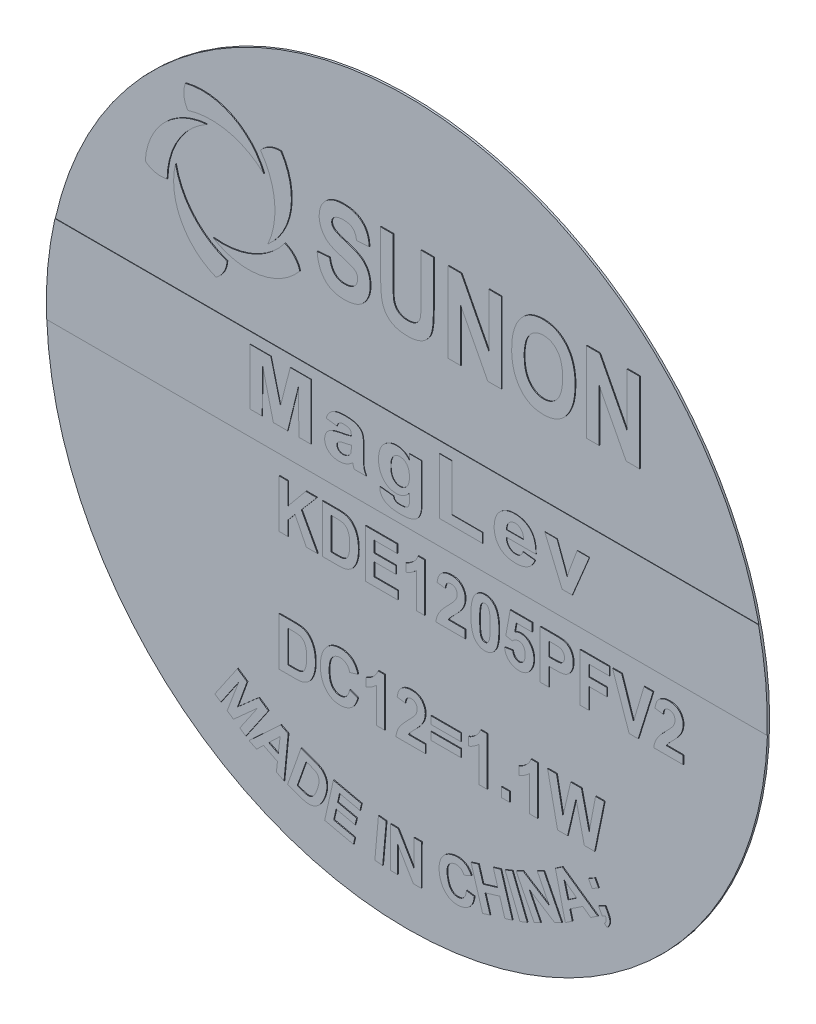
SolidWorks part; units mm, degrees
material "PET"
ref_plane "Front" through (0, 0, 0) normal (0, 0, 1) x (1, 0, 0)
ref_plane "Top" through (0, 0, 0) normal (0, 1, 0) x (1, 0, 0)
ref_plane "Right" through (0, 0, 0) normal (1, 0, 0) x (0, 0, -1)
sketch "Эскиз1" plane through (0, 0, 0) normal (0, 0, 1) x (1, 0, 0)
  circle A0 centre (0, 0) radius 9
  dimension "D1" = 18
extrude "Бобышка-Вытянуть1" add sketch "Эскиз1" along normal blind 0.05
sketch "Эскиз2" plane through (0, 0, 0.05) normal (0, 0, 1) x (1, 0, 0)
  arc A0 (-4.8588, -6.2452) -> (4.8833, -6.2452) centre (0.0123, -0.0965) ccw construction
  arc A2 (-5.5151, 6.5319) -> (-3.5562, 5.5539) centre (-5.0958, 4.9209) cw
  arc A4 (-5.4535, 5.9772) -> (-3.5562, 5.5539) centre (-4.8709, 4.1247) cw
  arc A5 (-5.5151, 6.5319) -> (-5.4535, 5.9772) centre (-4.9377, 6.3153) ccw
  circle A6 centre (-4.5148, 4.7517) radius 1.25 construction
  arc A7 (-3.1308, 6.2532) -> (-3.4556, 4.0879) centre (-4.5334, 5.3566) cw
  arc A8 (-3.1308, 6.2532) -> (-3.6393, 6.0232) centre (-3.1584, 5.6371) ccw
  arc A9 (-3.6393, 6.0232) -> (-3.4556, 4.0879) centre (-5.2212, 4.8967) cw
  arc A10 (-2.6591, 3.8995) -> (-4.8188, 3.5392) centre (-3.9453, 4.9563) cw
  arc A12 (-2.6591, 3.8995) -> (-3.035, 4.312) centre (-3.2536, 3.7353) ccw
  arc A15 (-3.035, 4.312) -> (-4.8188, 3.5392) centre (-4.5952, 5.4683) cw
  arc A16 (-4.7519, 2.7235) -> (-5.7619, 4.6662) centre (-4.1442, 4.2733) cw
  arc A17 (-4.7519, 2.7235) -> (-4.4757, 3.2084) centre (-5.0917, 3.2381) ccw
  arc A18 (-4.4757, 3.2084) -> (-5.7619, 4.6662) centre (-3.8581, 5.0496) cw
  arc A19 (-6.517, 4.3504) -> (-4.9815, 5.9113) centre (-4.8553, 4.2514) cw
  arc A20 (-6.517, 4.3504) -> (-5.9704, 4.2376) centre (-6.1326, 4.8327) ccw
  arc A21 (-5.9704, 4.2376) -> (-4.9815, 5.9113) centre (-4.0285, 4.2192) cw
  text T0 "SUNON" font "Arial Narrow" height 2
  text T1 "KDE1205PFV2\r\nDC12=1.1W" font "Arial Narrow" height 1.2
  text T2 "MADE IN CHINA;)" font "Arial Narrow" height 1
  text T3 "MagLev" font "Arial" height 1.4
  point P3 (0, 0)
  point P16 (-5.1102, 5.946)
  point P17 (-5.7604, 4.6474)
  point P40 (-4.5148, 4.7517)
  point P42 (-3.2536, -1.3591)
  point P44 (0, 0)
  point P45 (0, 0)
  point P46 (0, 0)
  point P47 (-3.2536, -1.6824)
  point P48 (0, 0)
  point P49 (-4.0285, 0.2962)
  point P50 (0, 0)
  dimension "D1" = 2.5
  dimension "D2" = 5
extrude "Бобышка-Вытянуть2" add sketch "Эскиз2" along normal blind 0.02
sketch "Эскиз3" plane through (0, 0, 0.05) normal (0, 0, 1) x (1, 0, 0)
  line L0 (-8.7818, 1.9697) -> (8.7818, 1.9697)
  line L1 (-10.1071, 1.9697) -> (9.8757, 1.9697) construction
  line L2 (-10.1071, 1.9697) -> (-10.1071, -0.3149) construction
  line L3 (-10.1071, -0.3149) -> (9.8757, -0.3149) construction
  line L4 (9.8757, 1.9697) -> (9.8757, -0.3149) construction
  line L5 (-0.1157, -0.3149) -> (-0.1157, 1.9697) construction
  line L6 (-10.1071, 0.8274) -> (9.8757, 0.8274) construction
  line L7 (-8.9945, -0.3149) -> (8.9945, -0.3149)
  circle A0 centre (0, 0) radius 9 construction
  arc A1 (-8.7818, 1.9697) -> (-8.9945, -0.3149) centre (0, 0) ccw
  arc A2 (8.7818, 1.9697) -> (8.9945, -0.3149) centre (0, 0) cw
  point P0 (-0.1157, 0.8274)
  dimension "D1" = 2.2846
  dimension "D2" = 19.9828
extrude "Бобышка-Вытянуть3" add sketch "Эскиз3" along normal blind 0.01
